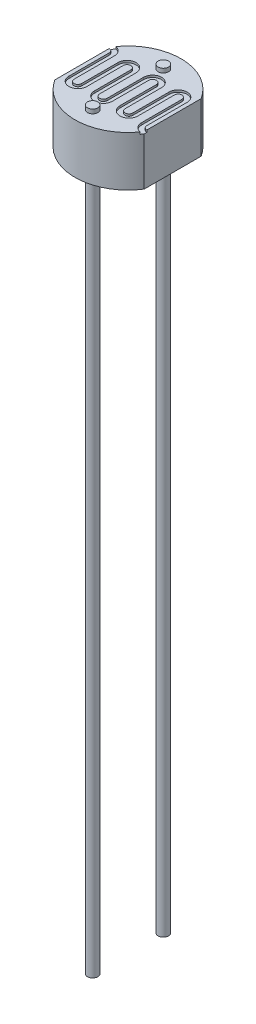
SolidWorks part; units mm, degrees
ref_plane "Front Plane" through (0, 0, 0) normal (0, 0, 1) x (1, 0, 0)
ref_plane "Top Plane" through (0, 0, 0) normal (0, 1, 0) x (1, 0, 0)
ref_plane "Right Plane" through (0, 0, 0) normal (1, 0, 0) x (0, 0, -1)
sketch "Sketch1" plane through (0, 0, 0) normal (0, 1, 0) x (1, 0, 0)
  line L0 (2.15, 1.3711) -> (2.15, -1.3711)
  line L1 (-2.15, 1.3711) -> (-2.15, -1.3711)
  line L2 (-2.15, 0) -> (2.15, 0) construction
  arc A0 (-2.15, -1.3711) -> (2.15, -1.3711) centre (0, 0) ccw
  arc A1 (2.15, 1.3711) -> (-2.15, 1.3711) centre (0, 0) ccw
  dimension "D2" = 5.1
  dimension "D1" = 4.3
extrude "Boss-Extrude1" add sketch "Sketch1" along normal blind 2.4
sketch "Sketch2" plane through (0, 0, 0) normal (0, -1, 0) x (1, 0, 0)
  line L0 (0, 1.7) -> (0, -1.7) construction
  circle A0 centre (0, 1.7) radius 0.25
  circle A1 centre (0, -1.7) radius 0.25
  dimension "D1" = 0.5
  dimension "D2" = 3.4
extrude "Boss-Extrude2" add sketch "Sketch2" along normal offset from surface (36.2 mm away) 36 from offset 2.6
sketch "Sketch3" plane through (0, 2.4, 0) normal (0, 1, 0) x (1, 0, 0)
  line L0 (-1.8429, 1.064) -> (-1.8429, -0.875)
  line L1 (-1.2286, -0.875) -> (-1.2286, 0.875)
  line L2 (-0.6143, 0.875) -> (-0.6143, -0.875)
  line L3 (0, -0.875) -> (0, 0.875)
  line L4 (0.6143, 0.875) -> (0.6143, -0.875)
  line L5 (1.2286, -0.875) -> (1.2286, 0.875)
  line L6 (1.8429, 0.875) -> (1.8429, -1.064)
  line L8 (-2.15, 1.3711) -> (-2.5287, 1.3711) construction
  line L9 (2.15, -1.3711) -> (2.6597, -1.3711) construction
  arc A0 (-1.8429, -0.875) -> (-1.2286, -0.875) centre (-1.5357, -0.875) ccw
  arc A1 (-1.2286, 0.875) -> (-0.6143, 0.875) centre (-0.9214, 0.875) cw
  arc A2 (-0.6143, -0.875) -> (0, -0.875) centre (-0.3071, -0.875) ccw
  arc A3 (0, 0.875) -> (0.6143, 0.875) centre (0.3071, 0.875) cw
  arc A4 (0.6143, -0.875) -> (1.2286, -0.875) centre (0.9214, -0.875) ccw
  arc A5 (1.2286, 0.875) -> (1.8429, 0.875) centre (1.5357, 0.875) cw
  arc A6 (1.8429, -1.064) -> (2.15, -1.3711) centre (2.15, -1.064) ccw
  arc A7 (-1.8429, 1.064) -> (-2.15, 1.3711) centre (-2.15, 1.064) ccw
  dimension "D1" = 1.75
extrude "Cut-Extrude-Thin1" cut sketch "Sketch3" against normal blind 0.1 thin thin type mid plane wall 0.25
